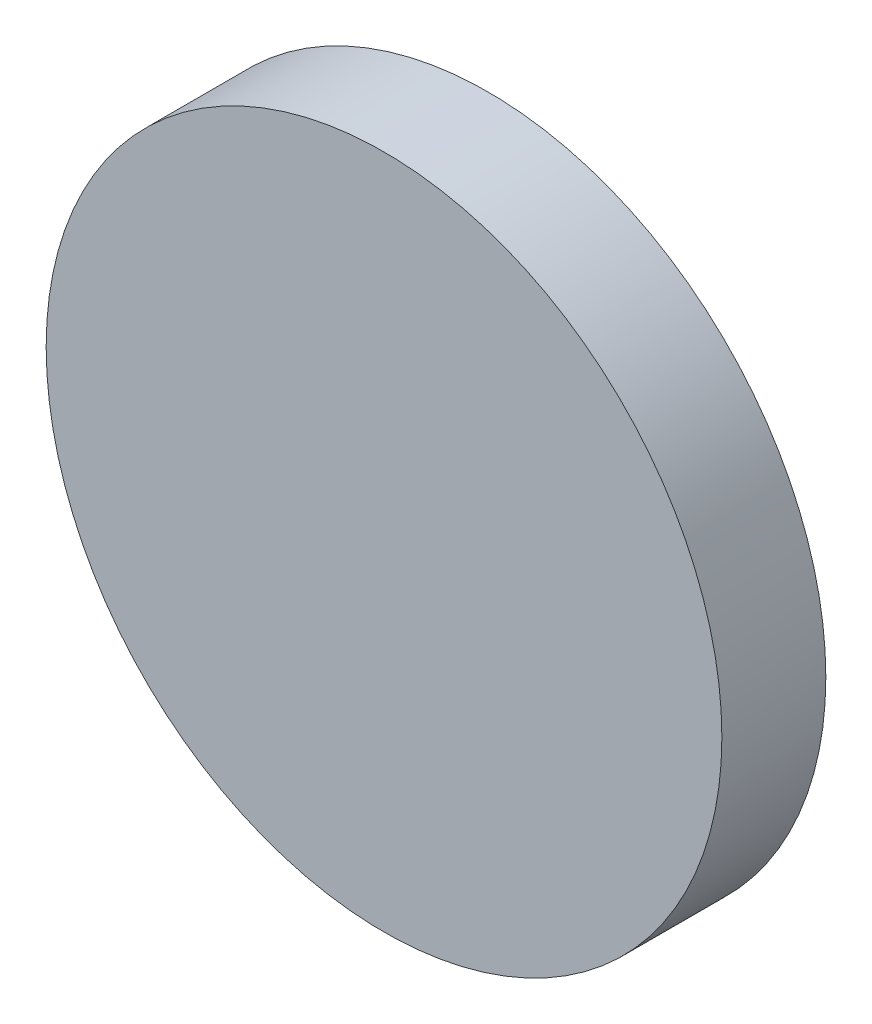
SolidWorks part; units mm, degrees
ref_plane "正面" through (0, 0, 0) normal (0, 0, 1) x (1, 0, 0)
ref_plane "平面" through (0, 0, 0) normal (0, 1, 0) x (1, 0, 0)
ref_plane "右側面" through (0, 0, 0) normal (1, 0, 0) x (0, 0, -1)
sketch "ｽｹｯﾁ1" plane through (0, 0, 0) normal (0, 0, 1) x (1, 0, 0)
  circle A0 centre (-26.1199, 17.9896) radius 32.5
  dimension "D1" = 65
extrude "ﾎﾞｽ - 押し出し1" add sketch "ｽｹｯﾁ1" along normal blind 10
